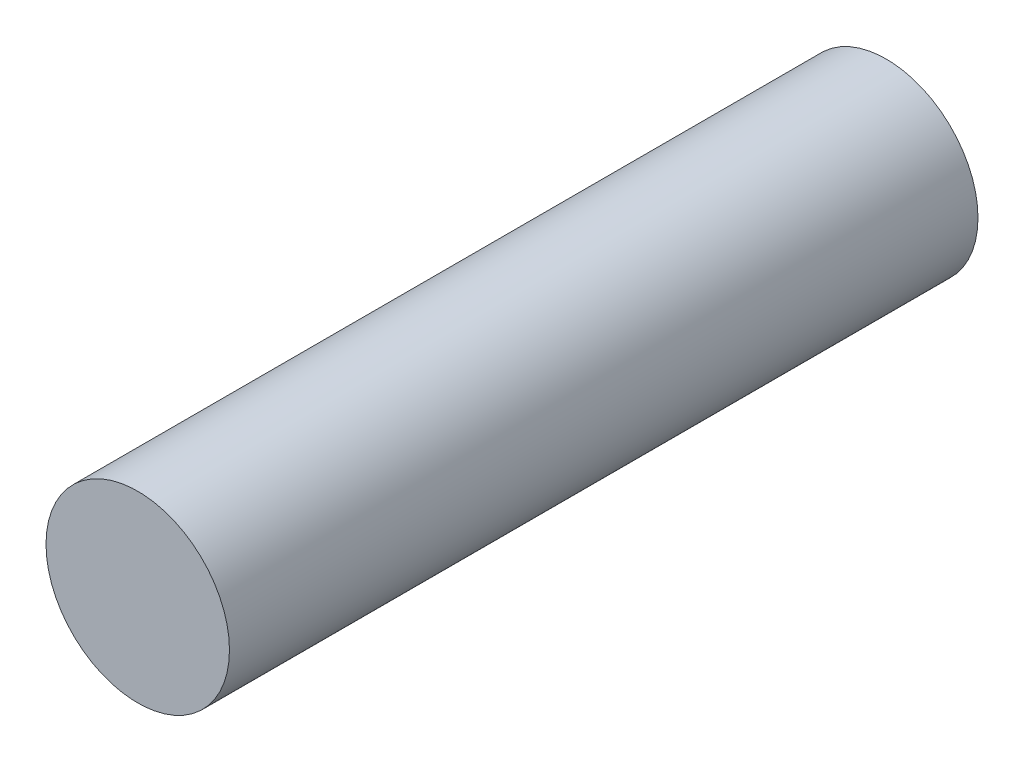
SolidWorks part; units mm, degrees
ref_plane "Front Plane" through (0, 0, 0) normal (0, 0, 1) x (1, 0, 0)
ref_plane "Top Plane" through (0, 0, 0) normal (0, 1, 0) x (1, 0, 0)
ref_plane "Right Plane" through (0, 0, 0) normal (1, 0, 0) x (0, 0, -1)
sketch "Sketch1" plane through (0, 0, 0) normal (0, 0, 1) x (1, 0, 0)
  circle A0 centre (0, 0) radius 5
  dimension "D1" = 10
extrude "Boss-Extrude1" add sketch "Sketch1" along normal blind 40.8
